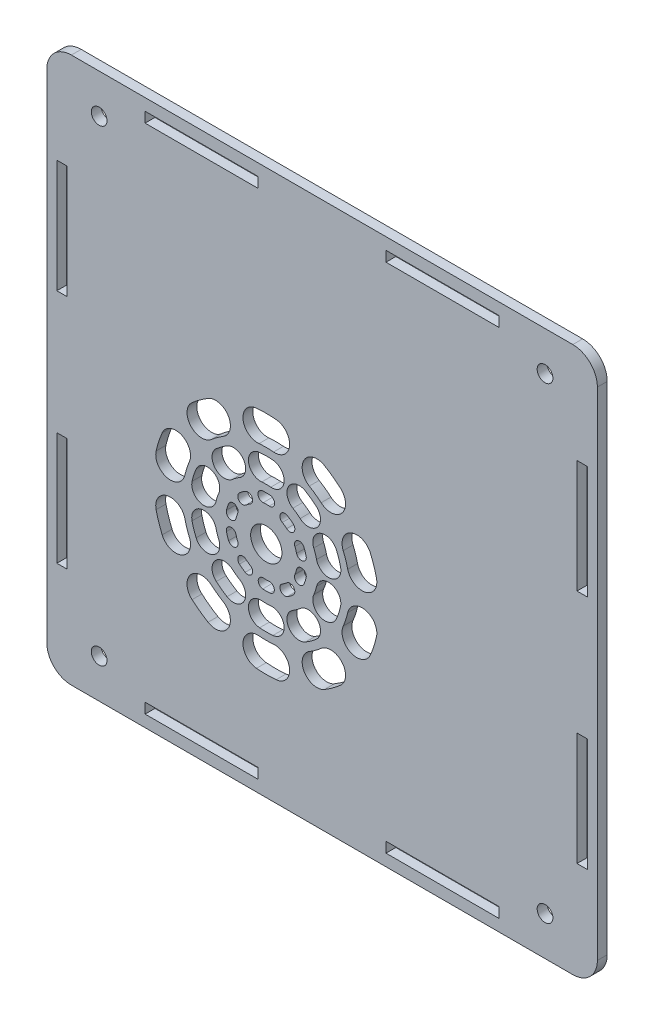
SolidWorks part; units mm, degrees
ref_plane "前视基准面" through (0, 0, 0) normal (0, 0, 1) x (1, 0, 0)
ref_plane "上视基准面" through (0, 0, 0) normal (0, 1, 0) x (1, 0, 0)
ref_plane "右视基准面" through (0, 0, 0) normal (1, 0, 0) x (0, 0, -1)
sketch "草图1" plane through (0, 0, 0) normal (0, 0, 1) x (1, 0, 0)
  line L1 (-56, 55.5) -> (56, 55.5)
  line L2 (-56, 55.5) -> (-56, -55.5)
  line L3 (-56, -55.5) -> (56, -55.5)
  line L4 (56, 55.5) -> (56, -55.5)
  line L5 (-56, 55.5) -> (56, -55.5) construction
  line L6 (-56, -55.5) -> (56, 55.5) construction
  point P0 (0, 0)
  dimension "D1" = 111
  dimension "D2" = 112
extrude "凸台-拉伸1" add sketch "草图1" along normal blind 2
sketch "草图2" plane through (0, 0, 0) normal (0, 0, -1) x (-1, 0, 0)
  circle A0 centre (-45.35, -47.55) radius 1.6
  circle A1 centre (45.35, -47.55) radius 1.6
  circle A2 centre (45.35, 47.55) radius 1.6
  circle A3 centre (-45.35, 47.55) radius 1.6
  dimension "D2" = 3.2
  dimension "D1" = 45.35
  dimension "D3" = 47.55
  dimension "D4" = 2
  dimension "D5" = 2
extrude "切除-拉伸1" cut sketch "草图2" against normal through all
sketch "草图3" plane through (0, 0, 0) normal (0, 0, -1) x (-1, 0, 0)
  line L0 (0, 0) -> (0, -29.5446) construction
  line L1 (0, 0) -> (30.314, 0) construction
  line L3 (-53.95, 35.5) -> (-51.85, 35.5)
  line L4 (-53.95, 35.5) -> (-53.95, 12.5)
  line L5 (-53.95, 12.5) -> (-51.85, 12.5)
  line L6 (-51.85, 35.5) -> (-51.85, 12.5)
  line L7 (-53.95, -12.5) -> (-51.85, -12.5)
  line L8 (-53.95, -12.5) -> (-53.95, -35.5)
  line L9 (-53.95, -35.5) -> (-51.85, -35.5)
  line L10 (-51.85, -12.5) -> (-51.85, -35.5)
  line L11 (56, -55.5) -> (-56, -55.5) construction
  line L12 (-56, 55.5) -> (56, 55.5) construction
  line L13 (51.85, -12.5) -> (51.85, -35.5)
  line L14 (53.95, -35.5) -> (51.85, -35.5)
  line L15 (53.95, -12.5) -> (53.95, -35.5)
  line L16 (53.95, -12.5) -> (51.85, -12.5)
  line L17 (51.85, 35.5) -> (51.85, 12.5)
  line L18 (53.95, 12.5) -> (51.85, 12.5)
  line L19 (53.95, 35.5) -> (53.95, 12.5)
  line L20 (53.95, 35.5) -> (51.85, 35.5)
  line L21 (-56, -55.5) -> (-56, 55.5) construction
  line L22 (-36, -51) -> (-13, -51)
  line L23 (-36, -51) -> (-36, -53.1)
  line L24 (-36, -53.1) -> (-13, -53.1)
  line L25 (-13, -51) -> (-13, -53.1)
  line L26 (13, -51) -> (36, -51)
  line L27 (13, -51) -> (13, -53.1)
  line L28 (13, -53.1) -> (36, -53.1)
  line L29 (36, -51) -> (36, -53.1)
  line L30 (56, 55.5) -> (56, -55.5) construction
  line L31 (36, 51) -> (36, 53.1)
  line L32 (13, 53.1) -> (36, 53.1)
  line L33 (13, 51) -> (13, 53.1)
  line L34 (13, 51) -> (36, 51)
  line L35 (-13, 51) -> (-13, 53.1)
  line L36 (-36, 53.1) -> (-13, 53.1)
  line L37 (-36, 51) -> (-36, 53.1)
  line L38 (-36, 51) -> (-13, 51)
  point P16 (-52.9, 35.5)
  dimension "D1" = 2.1
  dimension "D2" = 2.1
  dimension "D3" = 51.85
  dimension "D4" = 23
  dimension "D5" = 23
  dimension "D6" = 20
  dimension "D7" = 20
  dimension "D8" = 51
  dimension "D9" = 2.1
  dimension "D10" = 2.1
  dimension "D11" = 23
  dimension "D12" = 23
  dimension "D13" = 20
  dimension "D14" = 20
extrude "切除-拉伸2" cut sketch "草图3" against normal through all
sketch "草图4" plane through (0, 0, 2) normal (0, 0, 1) x (1, 0, 0)
  line L0 (-56, -55.5) -> (56, -55.5) construction
  line L1 (-56, 55.5) -> (-56, -55.5) construction
  line L2 (-13.0931, 9.1239) -> (-11.35, -10.8) construction
  line L3 (-11.35, -10.8) -> (-9.6069, 9.1239) construction
  line L4 (-11.35, -10.8) -> (-11.35, 9.2) construction
  line L7 (-11.35, -10.8) -> (8.65, -10.8) construction
  circle A0 centre (-11.35, -10.8) radius 20 construction
  arc A1 (-13.0931, 9.1239) -> (-9.6069, 9.1239) centre (-11.35, -10.8) cw construction
  arc A2 (-9.3454, 12.1125) -> (-13.3546, 12.1125) centre (-11.35, -10.8) ccw
  arc A3 (-9.8684, 6.1353) -> (-12.8316, 6.1353) centre (-11.35, -10.8) ccw
  arc A4 (-9.8684, 6.1353) -> (-9.3454, 12.1125) centre (-9.6069, 9.1239) ccw
  arc A5 (-13.3546, 12.1125) -> (-12.8316, 6.1353) centre (-13.0931, 9.1239) ccw
  arc A6 (-10.217, 2.1505) -> (-12.483, 2.1505) centre (-11.35, -10.8) ccw construction
  arc A7 (-9.9991, 4.641) -> (-12.7009, 4.641) centre (-11.35, -10.8) ccw
  arc A8 (-10.4349, -0.34) -> (-12.2651, -0.34) centre (-11.35, -10.8) ccw
  arc A9 (-10.4349, -0.34) -> (-9.9991, 4.641) centre (-10.217, 2.1505) ccw
  arc A10 (-12.7009, 4.641) -> (-12.2651, -0.34) centre (-12.483, 2.1505) ccw
  arc A11 (-12.0472, -2.8304) -> (-10.6528, -2.8304) centre (-11.35, -10.8) cw construction
  arc A12 (-10.5656, -1.8342) -> (-12.1344, -1.8342) centre (-11.35, -10.8) ccw
  arc A13 (-10.7399, -3.8266) -> (-11.9601, -3.8266) centre (-11.35, -10.8) ccw
  arc A14 (-10.7399, -3.8266) -> (-10.5656, -1.8342) centre (-10.6528, -2.8304) ccw
  arc A15 (-12.1344, -1.8342) -> (-11.9601, -3.8266) centre (-12.0472, -2.8304) ccw
  arc A16 (-1.0492, 6.3433) -> (1.7712, 4.2942) centre (-11.35, -10.8) cw construction
  arc A21 (3.7394, 6.5583) -> (0.4959, 8.9148) centre (-11.35, -10.8) ccw
  arc A26 (-0.197, 2.0301) -> (-2.5944, 3.7718) centre (-11.35, -10.8) ccw
  arc A31 (-0.197, 2.0301) -> (3.7394, 6.5583) centre (1.7712, 4.2942) ccw
  arc A36 (0.4959, 8.9148) -> (-2.5944, 3.7718) centre (-1.0492, 6.3433) ccw
  arc A41 (-2.8212, -0.9888) -> (-4.6545, 0.3432) centre (-11.35, -10.8) ccw construction
  arc A46 (-1.1811, 0.898) -> (-3.3669, 2.4861) centre (-11.35, -10.8) ccw
  arc A51 (-4.4614, -2.8755) -> (-5.9421, -1.7997) centre (-11.35, -10.8) ccw
  arc A56 (-4.4614, -2.8755) -> (-1.1811, 0.898) centre (-2.8212, -0.9888) ccw
  arc A62 (-3.3669, 2.4861) -> (-5.9421, -1.7997) centre (-4.6545, 0.3432) ccw
  arc A63 (-7.5793, -4.5246) -> (-6.5469, -5.2747) centre (-11.35, -10.8) cw construction
  arc A64 (-5.8909, -4.52) -> (-7.0643, -3.6674) centre (-11.35, -10.8) ccw
  arc A65 (-7.203, -6.0294) -> (-8.0944, -5.3817) centre (-11.35, -10.8) ccw
  arc A66 (-7.203, -6.0294) -> (-5.8909, -4.52) centre (-6.5469, -5.2747) ccw
  arc A67 (-7.0643, -3.6674) -> (-8.0944, -5.3817) centre (-7.5793, -4.5246) ccw
  arc A68 (7.0601, -2.9854) -> (8.1374, -6.301) centre (-11.35, -10.8) cw construction
  arc A69 (11.0605, -5.6261) -> (9.8216, -1.8132) centre (-11.35, -10.8) ccw
  arc A70 (5.2143, -6.9758) -> (4.2986, -4.1576) centre (-11.35, -10.8) ccw
  arc A71 (5.2143, -6.9758) -> (11.0605, -5.6261) centre (8.1374, -6.301) ccw
  arc A72 (9.8216, -1.8132) -> (4.2986, -4.1576) centre (7.0601, -2.9854) ccw
  arc A73 (1.3168, -7.8756) -> (0.6166, -5.7205) centre (-11.35, -10.8) ccw construction
  arc A74 (3.7527, -7.3133) -> (2.9178, -4.7437) centre (-11.35, -10.8) ccw
  arc A75 (-1.1191, -8.438) -> (-1.6847, -6.6973) centre (-11.35, -10.8) ccw
  arc A76 (-1.1191, -8.438) -> (3.7527, -7.3133) centre (1.3168, -7.8756) ccw
  arc A77 (2.9178, -4.7437) -> (-1.6847, -6.6973) centre (0.6166, -5.7205) ccw
  arc A78 (-4.6109, -7.9394) -> (-4.2165, -9.1531) centre (-11.35, -10.8) cw construction
  arc A79 (-3.2421, -8.9282) -> (-3.6904, -7.5487) centre (-11.35, -10.8) ccw
  arc A80 (-5.1909, -9.3781) -> (-5.5314, -8.3301) centre (-11.35, -10.8) ccw
  arc A81 (-5.1909, -9.3781) -> (-3.2421, -8.9282) centre (-4.2165, -9.1531) ccw
  arc A82 (-3.6904, -7.5487) -> (-5.5314, -8.3301) centre (-4.6109, -7.9394) ccw
  arc A83 (8.1374, -15.299) -> (7.0601, -18.6146) centre (-11.35, -10.8) cw construction
  arc A84 (9.8216, -19.7868) -> (11.0605, -15.9739) centre (-11.35, -10.8) ccw
  arc A85 (4.2986, -17.4424) -> (5.2143, -14.6242) centre (-11.35, -10.8) ccw
  arc A86 (4.2986, -17.4424) -> (9.8216, -19.7868) centre (7.0601, -18.6146) ccw
  arc A87 (11.0605, -15.9739) -> (5.2143, -14.6242) centre (8.1374, -15.299) ccw
  arc A88 (0.6166, -15.8795) -> (1.3168, -13.7244) centre (-11.35, -10.8) ccw construction
  arc A89 (2.9178, -16.8563) -> (3.7527, -14.2867) centre (-11.35, -10.8) ccw
  arc A90 (-1.6847, -14.9027) -> (-1.1191, -13.162) centre (-11.35, -10.8) ccw
  arc A91 (-1.6847, -14.9027) -> (2.9178, -16.8563) centre (0.6166, -15.8795) ccw
  arc A92 (3.7527, -14.2867) -> (-1.1191, -13.162) centre (1.3168, -13.7244) ccw
  arc A93 (-4.2165, -12.4469) -> (-4.6109, -13.6606) centre (-11.35, -10.8) cw construction
  arc A94 (-3.6904, -14.0513) -> (-3.2421, -12.6718) centre (-11.35, -10.8) ccw
  arc A95 (-5.5314, -13.2699) -> (-5.1909, -12.2219) centre (-11.35, -10.8) ccw
  arc A96 (-5.5314, -13.2699) -> (-3.6904, -14.0513) centre (-4.6109, -13.6606) ccw
  arc A97 (-3.2421, -12.6718) -> (-5.1909, -12.2219) centre (-4.2165, -12.4469) ccw
  arc A98 (1.7712, -25.8942) -> (-1.0492, -27.9433) centre (-11.35, -10.8) cw construction
  arc A99 (0.4959, -30.5148) -> (3.7394, -28.1583) centre (-11.35, -10.8) ccw
  arc A100 (-2.5944, -25.3718) -> (-0.197, -23.6301) centre (-11.35, -10.8) ccw
  arc A101 (-2.5944, -25.3718) -> (0.4959, -30.5148) centre (-1.0492, -27.9433) ccw
  arc A102 (3.7394, -28.1583) -> (-0.197, -23.6301) centre (1.7712, -25.8942) ccw
  arc A103 (-4.6545, -21.9432) -> (-2.8212, -20.6112) centre (-11.35, -10.8) ccw construction
  arc A104 (-3.3669, -24.0861) -> (-1.1811, -22.498) centre (-11.35, -10.8) ccw
  arc A105 (-5.9421, -19.8003) -> (-4.4614, -18.7245) centre (-11.35, -10.8) ccw
  arc A106 (-5.9421, -19.8003) -> (-3.3669, -24.0861) centre (-4.6545, -21.9432) ccw
  arc A107 (-1.1811, -22.498) -> (-4.4614, -18.7245) centre (-2.8212, -20.6112) ccw
  arc A108 (-6.5469, -16.3253) -> (-7.5793, -17.0754) centre (-11.35, -10.8) cw construction
  arc A109 (-7.0643, -17.9326) -> (-5.8909, -17.08) centre (-11.35, -10.8) ccw
  arc A110 (-8.0944, -16.2183) -> (-7.203, -15.5706) centre (-11.35, -10.8) ccw
  arc A111 (-8.0944, -16.2183) -> (-7.0643, -17.9326) centre (-7.5793, -17.0754) ccw
  arc A112 (-5.8909, -17.08) -> (-7.203, -15.5706) centre (-6.5469, -16.3253) ccw
  arc A113 (-9.6069, -30.7239) -> (-13.0931, -30.7239) centre (-11.35, -10.8) cw construction
  arc A114 (-13.3546, -33.7125) -> (-9.3454, -33.7125) centre (-11.35, -10.8) ccw
  arc A115 (-12.8316, -27.7353) -> (-9.8684, -27.7353) centre (-11.35, -10.8) ccw
  arc A116 (-12.8316, -27.7353) -> (-13.3546, -33.7125) centre (-13.0931, -30.7239) ccw
  arc A117 (-9.3454, -33.7125) -> (-9.8684, -27.7353) centre (-9.6069, -30.7239) ccw
  arc A118 (-12.483, -23.7505) -> (-10.217, -23.7505) centre (-11.35, -10.8) ccw construction
  arc A119 (-12.7009, -26.241) -> (-9.9991, -26.241) centre (-11.35, -10.8) ccw
  arc A120 (-12.2651, -21.26) -> (-10.4349, -21.26) centre (-11.35, -10.8) ccw
  arc A121 (-12.2651, -21.26) -> (-12.7009, -26.241) centre (-12.483, -23.7505) ccw
  arc A122 (-9.9991, -26.241) -> (-10.4349, -21.26) centre (-10.217, -23.7505) ccw
  arc A123 (-10.7119, -18.0933) -> (-11.9881, -18.0933) centre (-11.35, -10.8) cw construction
  arc A124 (-12.0752, -19.0895) -> (-10.6248, -19.0895) centre (-11.35, -10.8) ccw
  arc A125 (-11.9009, -17.0971) -> (-10.7991, -17.0971) centre (-11.35, -10.8) ccw
  arc A126 (-11.9009, -17.0971) -> (-12.0752, -19.0895) centre (-11.9881, -18.0933) ccw
  arc A127 (-10.6248, -19.0895) -> (-10.7991, -17.0971) centre (-10.7119, -18.0933) ccw
  arc A128 (-21.6508, -27.9433) -> (-24.4712, -25.8942) centre (-11.35, -10.8) cw construction
  arc A129 (-26.4394, -28.1583) -> (-23.1959, -30.5148) centre (-11.35, -10.8) ccw
  arc A130 (-22.503, -23.6301) -> (-20.1056, -25.3718) centre (-11.35, -10.8) ccw
  arc A131 (-22.503, -23.6301) -> (-26.4394, -28.1583) centre (-24.4712, -25.8942) ccw
  arc A132 (-23.1959, -30.5148) -> (-20.1056, -25.3718) centre (-21.6508, -27.9433) ccw
  arc A133 (-19.8788, -20.6112) -> (-18.0455, -21.9432) centre (-11.35, -10.8) ccw construction
  arc A134 (-21.5189, -22.498) -> (-19.3331, -24.0861) centre (-11.35, -10.8) ccw
  arc A135 (-18.2386, -18.7245) -> (-16.7579, -19.8003) centre (-11.35, -10.8) ccw
  arc A136 (-18.2386, -18.7245) -> (-21.5189, -22.498) centre (-19.8788, -20.6112) ccw
  arc A137 (-19.3331, -24.0861) -> (-16.7579, -19.8003) centre (-18.0455, -21.9432) ccw
  arc A138 (-15.1207, -17.0754) -> (-16.1531, -16.3253) centre (-11.35, -10.8) cw construction
  arc A139 (-16.8091, -17.08) -> (-15.6357, -17.9326) centre (-11.35, -10.8) ccw
  arc A140 (-15.497, -15.5706) -> (-14.6056, -16.2183) centre (-11.35, -10.8) ccw
  arc A141 (-15.497, -15.5706) -> (-16.8091, -17.08) centre (-16.1531, -16.3253) ccw
  arc A142 (-15.6357, -17.9326) -> (-14.6056, -16.2183) centre (-15.1207, -17.0754) ccw
  arc A143 (-29.7601, -18.6146) -> (-30.8374, -15.299) centre (-11.35, -10.8) cw construction
  arc A144 (-33.7605, -15.9739) -> (-32.5216, -19.7868) centre (-11.35, -10.8) ccw
  arc A145 (-27.9143, -14.6242) -> (-26.9986, -17.4424) centre (-11.35, -10.8) ccw
  arc A146 (-27.9143, -14.6242) -> (-33.7605, -15.9739) centre (-30.8374, -15.299) ccw
  arc A147 (-32.5216, -19.7868) -> (-26.9986, -17.4424) centre (-29.7601, -18.6146) ccw
  arc A148 (-24.0168, -13.7244) -> (-23.3166, -15.8795) centre (-11.35, -10.8) ccw construction
  arc A149 (-26.4527, -14.2867) -> (-25.6178, -16.8563) centre (-11.35, -10.8) ccw
  arc A150 (-21.5809, -13.162) -> (-21.0153, -14.9027) centre (-11.35, -10.8) ccw
  arc A151 (-21.5809, -13.162) -> (-26.4527, -14.2867) centre (-24.0168, -13.7244) ccw
  arc A152 (-25.6178, -16.8563) -> (-21.0153, -14.9027) centre (-23.3166, -15.8795) ccw
  arc A153 (-18.0891, -13.6606) -> (-18.4835, -12.4469) centre (-11.35, -10.8) cw construction
  arc A154 (-19.4579, -12.6718) -> (-19.0096, -14.0513) centre (-11.35, -10.8) ccw
  arc A155 (-17.5091, -12.2219) -> (-17.1686, -13.2699) centre (-11.35, -10.8) ccw
  arc A156 (-17.5091, -12.2219) -> (-19.4579, -12.6718) centre (-18.4835, -12.4469) ccw
  arc A157 (-19.0096, -14.0513) -> (-17.1686, -13.2699) centre (-18.0891, -13.6606) ccw
  arc A158 (-30.8374, -6.301) -> (-29.7601, -2.9854) centre (-11.35, -10.8) cw construction
  arc A159 (-32.5216, -1.8132) -> (-33.7605, -5.6261) centre (-11.35, -10.8) ccw
  arc A160 (-26.9986, -4.1576) -> (-27.9143, -6.9758) centre (-11.35, -10.8) ccw
  arc A161 (-26.9986, -4.1576) -> (-32.5216, -1.8132) centre (-29.7601, -2.9854) ccw
  arc A162 (-33.7605, -5.6261) -> (-27.9143, -6.9758) centre (-30.8374, -6.301) ccw
  arc A163 (-23.3166, -5.7205) -> (-24.0168, -7.8756) centre (-11.35, -10.8) ccw construction
  arc A164 (-25.6178, -4.7437) -> (-26.4527, -7.3133) centre (-11.35, -10.8) ccw
  arc A165 (-21.0153, -6.6973) -> (-21.5809, -8.438) centre (-11.35, -10.8) ccw
  arc A166 (-21.0153, -6.6973) -> (-25.6178, -4.7437) centre (-23.3166, -5.7205) ccw
  arc A167 (-26.4527, -7.3133) -> (-21.5809, -8.438) centre (-24.0168, -7.8756) ccw
  arc A168 (-18.4835, -9.1531) -> (-18.0891, -7.9394) centre (-11.35, -10.8) cw construction
  arc A169 (-19.0096, -7.5487) -> (-19.4579, -8.9282) centre (-11.35, -10.8) ccw
  arc A170 (-17.1686, -8.3301) -> (-17.5091, -9.3781) centre (-11.35, -10.8) ccw
  arc A171 (-17.1686, -8.3301) -> (-19.0096, -7.5487) centre (-18.0891, -7.9394) ccw
  arc A172 (-19.4579, -8.9282) -> (-17.5091, -9.3781) centre (-18.4835, -9.1531) ccw
  arc A173 (-24.4712, 4.2942) -> (-21.6508, 6.3433) centre (-11.35, -10.8) cw construction
  arc A174 (-23.1959, 8.9148) -> (-26.4394, 6.5583) centre (-11.35, -10.8) ccw
  arc A175 (-20.1056, 3.7718) -> (-22.503, 2.0301) centre (-11.35, -10.8) ccw
  arc A176 (-20.1056, 3.7718) -> (-23.1959, 8.9148) centre (-21.6508, 6.3433) ccw
  arc A177 (-26.4394, 6.5583) -> (-22.503, 2.0301) centre (-24.4712, 4.2942) ccw
  arc A178 (-18.0455, 0.3432) -> (-19.8788, -0.9888) centre (-11.35, -10.8) ccw construction
  arc A179 (-19.3331, 2.4861) -> (-21.5189, 0.898) centre (-11.35, -10.8) ccw
  arc A180 (-16.7579, -1.7997) -> (-18.2386, -2.8755) centre (-11.35, -10.8) ccw
  arc A181 (-16.7579, -1.7997) -> (-19.3331, 2.4861) centre (-18.0455, 0.3432) ccw
  arc A182 (-21.5189, 0.898) -> (-18.2386, -2.8755) centre (-19.8788, -0.9888) ccw
  arc A183 (-16.1531, -5.2747) -> (-15.1207, -4.5246) centre (-11.35, -10.8) cw construction
  arc A184 (-15.6357, -3.6674) -> (-16.8091, -4.52) centre (-11.35, -10.8) ccw
  arc A185 (-14.6056, -5.3817) -> (-15.497, -6.0294) centre (-11.35, -10.8) ccw
  arc A186 (-14.6056, -5.3817) -> (-15.6357, -3.6674) centre (-15.1207, -4.5246) ccw
  arc A187 (-16.8091, -4.52) -> (-15.497, -6.0294) centre (-16.1531, -5.2747) ccw
  circle A188 centre (-11.35, -10.8) radius 3.181
  point P8 (-11.35, 9.2)
  point P19 (-11.35, 2.2)
  point P27 (-11.35, -2.8)
  point P37 (0.4057, 5.3803)
  point P44 (-3.7088, -0.2828)
  point P52 (-7.0467, -4.8771)
  point P59 (7.6711, -4.6197)
  point P66 (1.0137, -6.7828)
  point P73 (-4.3872, -8.5376)
  point P80 (7.6711, -16.9803)
  point P87 (1.0137, -14.8172)
  point P94 (-4.3872, -13.0624)
  point P101 (0.4057, -26.9803)
  point P108 (-3.7088, -21.3172)
  point P115 (-7.0467, -16.7229)
  point P122 (-11.35, -30.8)
  point P129 (-11.35, -23.8)
  point P136 (-11.35, -18.1211)
  point P143 (-23.1057, -26.9803)
  point P150 (-18.9912, -21.3172)
  point P157 (-15.6533, -16.7229)
  point P164 (-30.3711, -16.9803)
  point P171 (-23.7137, -14.8172)
  point P178 (-18.3128, -13.0624)
  point P185 (-30.3711, -4.6197)
  point P192 (-23.7137, -6.7828)
  point P199 (-18.3128, -8.5376)
  point P206 (-23.1057, 5.3803)
  point P213 (-18.9912, -0.2828)
  point P220 (-15.6533, -4.8771)
  point P225 (-11.35, -10.8)
  dimension "D3" = 40
  dimension "D5" = 3
  dimension "D6" = 2.5
  dimension "D8" = 5
  dimension "D7" = 7
  dimension "D9" = 1
  dimension "D10" = 1
  dimension "D1" = 44.7
  dimension "D2" = 44.65
  dimension "D4" = 5
extrude "切除-拉伸4" cut sketch "草图4" against normal blind 10
fillet "圆角1" radius 5 4 edges at (56, -55.5, 1) (-56, -55.5, 1) (-56, 55.5, 1) (56, 55.5, 1)
